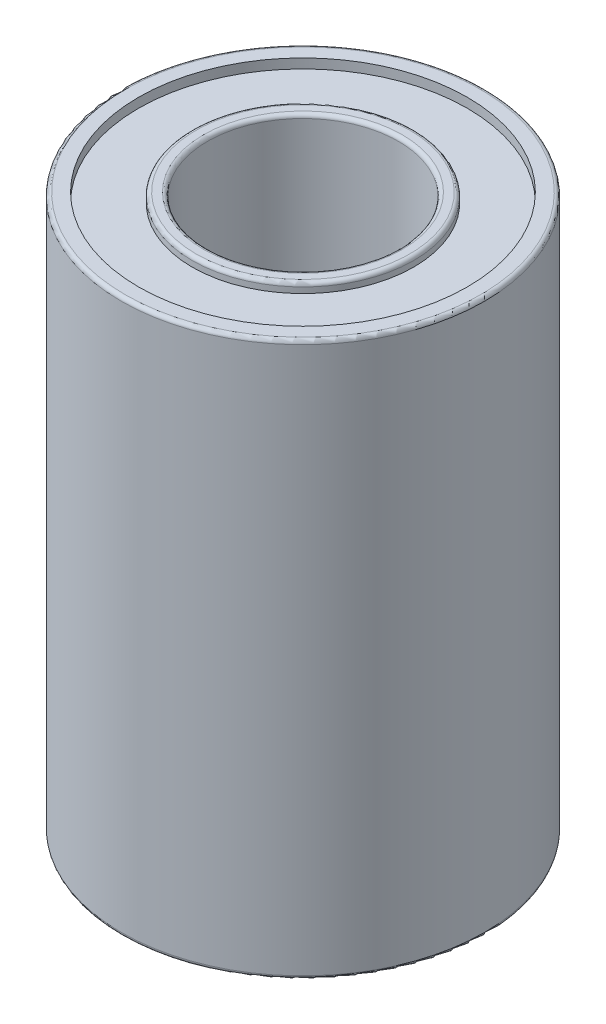
SolidWorks part; units mm, degrees
ref_plane "Front Plane" through (0, 0, 0) normal (0, 0, 1) x (1, 0, 0)
ref_plane "Top Plane" through (0, 0, 0) normal (0, 1, 0) x (1, 0, 0)
ref_plane "Right Plane" through (0, 0, 0) normal (1, 0, 0) x (0, 0, -1)
sketch "Sketch1" plane through (0, 0, 0) normal (0, 1, 0) x (1, 0, 0)
  circle A0 centre (0, 0) radius 9.5
  circle A1 centre (0, 0) radius 5
  dimension "D1" = 19
  dimension "D2" = 10
extrude "Boss-Extrude1" add sketch "Sketch1" along normal blind 29
sketch "Sketch2" plane through (0, 29, 0) normal (0, 1, 0) x (1, 0, 0)
  circle A0 centre (0, 0) radius 5 construction
  circle A1 centre (0, 0) radius 5
  circle A2 centre (0, 0) radius 5.8
  circle A3 centre (0, 0) radius 8.6
  dimension "D1" = 0.8
  dimension "D2" = 2.8
extrude "Cut-Extrude1" cut sketch "Sketch2" against normal blind 0.5 contours A3 A2
sketch "Sketch3" plane through (0, 0, 0) normal (0, -1, 0) x (1, 0, 0)
  circle A0 centre (0, 0) radius 5.8 construction
  circle A1 centre (0, 0) radius 8.6
  circle A2 centre (0, 0) radius 8.6
  circle A3 centre (0, 0) radius 5.8
  dimension "D1" = 0
extrude "Cut-Extrude2" cut sketch "Sketch3" against normal blind 0.5
fillet "Fillet1" radius 0.2
